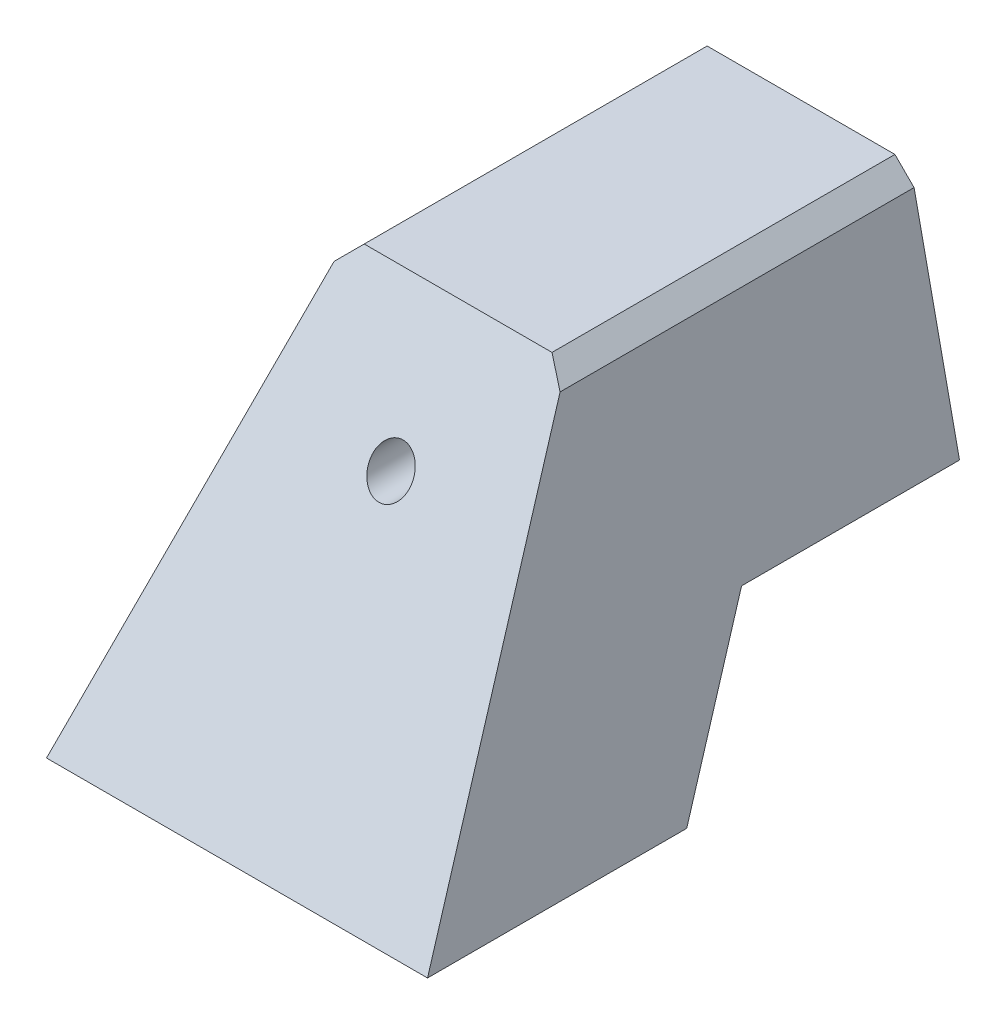
SolidWorks part; units mm, degrees
ref_plane "Front Plane" through (0, 0, 0) normal (0, 0, 1) x (1, 0, 0)
ref_plane "Top Plane" through (0, 0, 0) normal (0, 1, 0) x (1, 0, 0)
ref_plane "Right Plane" through (0, 0, 0) normal (1, 0, 0) x (0, 0, -1)
sketch "Sketch1" plane through (0, 0, 0) normal (0, 0, 1) x (1, 0, 0)
  line L0 (-25, -35) -> (-14.832, 12.7391)
  line L1 (-10.25, -10.25) -> (10.25, -10.25)
  line L2 (-10.25, -10.25) -> (-10.25, 10.25)
  line L3 (-10.25, 10.25) -> (10.25, 10.25)
  line L4 (10.25, -10.25) -> (10.25, 10.25)
  line L5 (-10.25, -10.25) -> (10.25, 10.25) construction
  line L6 (-10.25, 10.25) -> (10.25, -10.25) construction
  line L7 (-14.832, 12.7391) -> (-12.3211, 15.25)
  line L8 (-12.3211, 15.25) -> (12.3211, 15.25)
  line L9 (12.3211, 15.25) -> (14.832, 12.7391)
  line L10 (14.832, 12.7391) -> (25, -35)
  line L11 (25, -35) -> (-25, -35)
  line L12 (0, 0) -> (0, 15.25) construction
  line L13 (-14.832, 12.7391) -> (14.832, 12.7391) construction
  line L14 (0, 0) -> (0, -35) construction
  circle A0 centre (-10.25, 10.25) radius 5 construction
  point P0 (0, 0)
  point P13 (-32.9904, -47.3177)
  dimension "D3" = 5
  dimension "D1" = 20.5
  dimension "D2" = 35
  dimension "D4" = 50
extrude "Boss-Extrude1" add sketch "Sketch1" along normal blind 75
sketch "Sketch2" plane through (0, 0, 75) normal (0, 0, 1) x (1, 0, 0)
  line L1 (-10.25, 10.25) -> (10.25, 10.25)
  line L2 (-10.25, 10.25) -> (-10.25, -10.25)
  line L3 (-10.25, -10.25) -> (10.25, -10.25)
  line L4 (10.25, 10.25) -> (10.25, -10.25)
  circle A0 centre (0, 0) radius 2.75
  dimension "D1" = 5.5
extrude "Boss-Extrude2" add sketch "Sketch2" against normal offset from surface (35 mm away) 40 up to face at (0, -2.337, 0)
sketch "Sketch3" plane through (0, 0, 0) normal (1, 0, 0) x (0, 0, -1)
  line L0 (0, -15.25) -> (-28.5973, -15.25)
  line L1 (0, -35) -> (0, 12.7391) construction
  line L2 (-28.5973, -15.25) -> (-40, -35)
  line L3 (-75, -35) -> (0, -35) construction
  line L4 (-40, -35) -> (0, -35)
  line L5 (0, -35) -> (0, -15.25)
  line L6 (-45, 15.25) -> (-75, -36.7115)
  line L7 (-75, 15.25) -> (0, 15.25) construction
  line L8 (-75, -35) -> (-75, 12.7391) construction
  line L9 (-75, -36.7115) -> (-75, 15.25)
  line L10 (-75, 15.25) -> (-45, 15.25)
  line L11 (-40, 10.25) -> (-40, -10.25) construction
  line L12 (-40, -10.25) -> (0, -10.25) construction
  dimension "D1" = 5
  dimension "D2" = 5
  dimension "D3" = 60
  dimension "D4" = 35
extrude "Cut-Extrude1" cut sketch "Sketch3" against normal through all both and the other way through all
